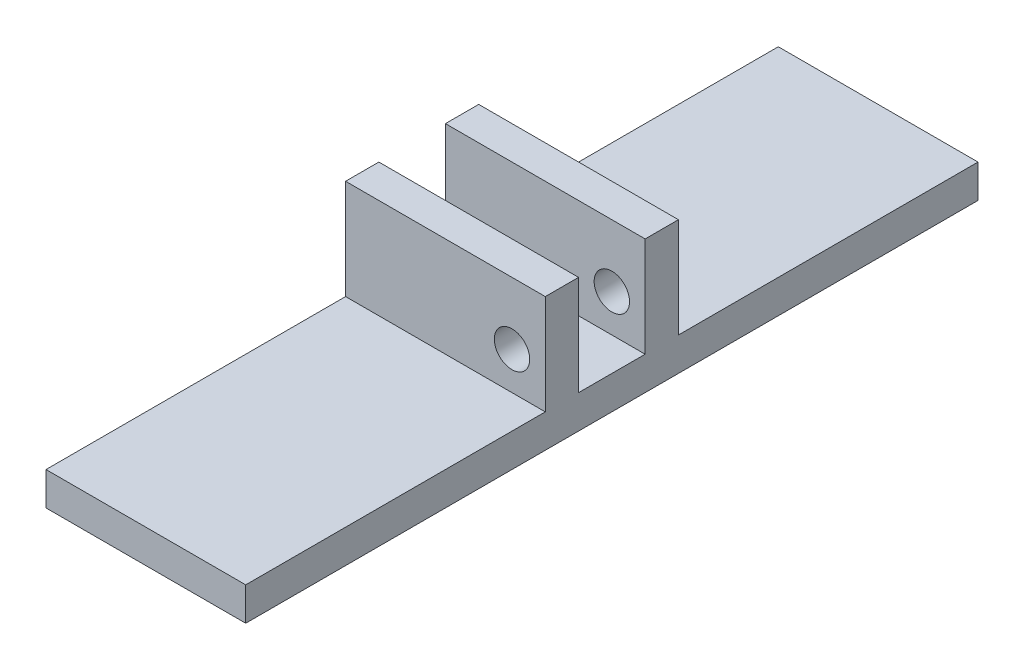
SolidWorks part; units mm, degrees
material "1060 Alloy"
ref_plane "Front Plane" through (0, 0, 0) normal (0, 0, 1) x (1, 0, 0)
ref_plane "Top Plane" through (0, 0, 0) normal (0, 1, 0) x (1, 0, 0)
ref_plane "Right Plane" through (0, 0, 0) normal (1, 0, 0) x (0, 0, -1)
sketch "Sketch1" plane through (0, 0, 0) normal (1, 0, 0) x (0, 0, -1)
  line L11 (-69.85, 0) -> (69.85, 0)
  line L14 (69.85, 0) -> (69.85, 6.35)
  line L17 (69.85, 6.35) -> (12.7, 6.35)
  line L18 (12.7, 6.35) -> (12.7, 25.4)
  line L19 (12.7, 25.4) -> (6.35, 25.4)
  line L20 (6.35, 25.4) -> (6.35, 6.35)
  line L21 (6.35, 6.35) -> (-6.35, 6.35)
  line L22 (-6.35, 6.35) -> (-6.35, 25.4)
  line L23 (-6.35, 25.4) -> (-12.7, 25.4)
  line L24 (-12.7, 25.4) -> (-12.7, 6.35)
  line L25 (-12.7, 6.35) -> (-69.85, 6.35)
  line L26 (-69.85, 6.35) -> (-69.85, 0)
  point P2 (0, 6.35)
  point P13 (0, 0)
  dimension "D1" = 6.35
  dimension "D2" = 139.7
  dimension "D4" = 6.35
  dimension "D3" = 12.7
  dimension "D5" = 19.05
extrude "Boss-Extrude1" add sketch "Sketch1" along normal blind 38.1
hole_wizard "1/4 Clearance Hole3" positions "Sketch6" profile "Sketch8" hole size "1/4" standard "ANSI Inch" end condition through all
sketch "Sketch6" plane through (0, 0, 12.7) normal (0, 0, 1) x (1, 0, 0)
  line L0 (38.1, 6.35) -> (0, 6.35) construction
  line L1 (38.1, 25.4) -> (38.1, 6.35) construction
  point P0 (31.75, 13.5255)
  dimension "D1" = 7.1755
  dimension "D2" = 6.35
sketch "Sketch8" plane through (31.75, 13.5255, 12.7) normal (1, 0, 0) x (0, -1, 0)
  line L0 (0, 0) -> (0, 82.55)
  line L1 (0, 82.55) -> (3.3782, 82.55)
  line L2 (3.3782, 82.55) -> (3.3782, 0)
  line L5 (3.3782, 0) -> (0, 0)
  line L11 (0, -6.35) -> (0, 107.95) construction
  dimension "Thru Hole Dia." = 6.7564
  dimension "Thru Hole Depth" = 82.55
